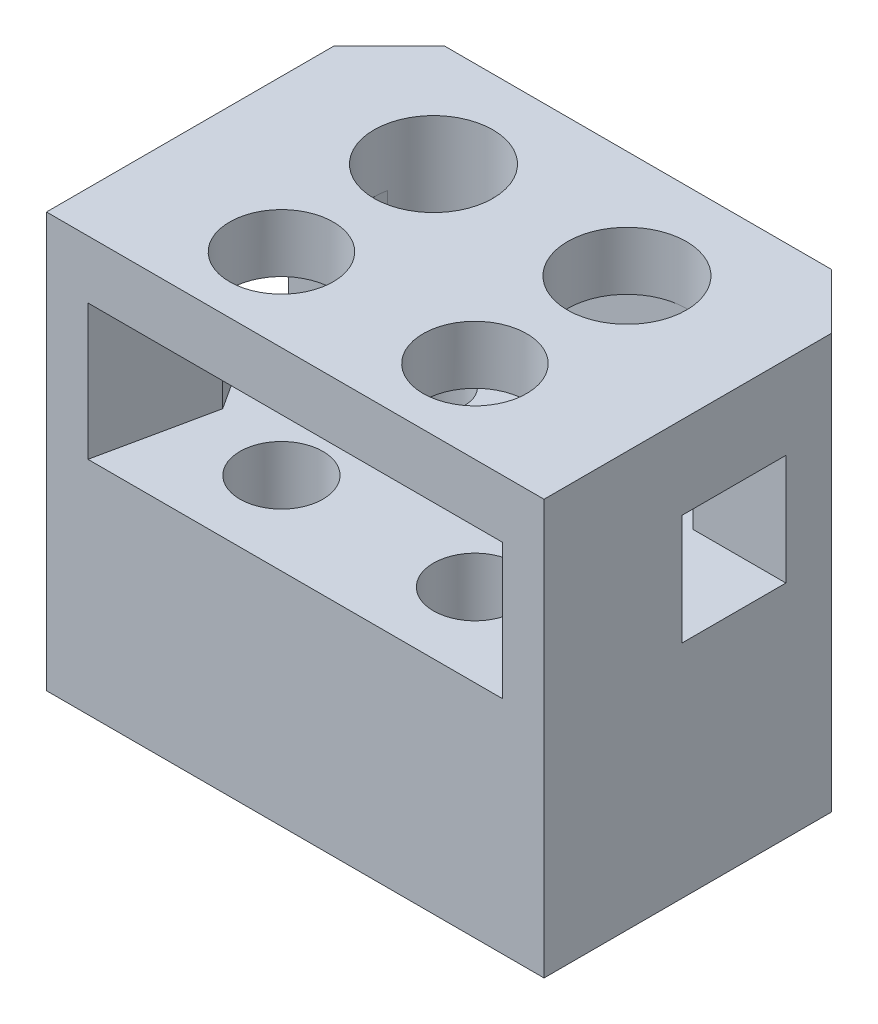
SolidWorks part; units mm, degrees
ref_plane "Front Plane" through (0, 0, 0) normal (0, 0, 1) x (1, 0, 0)
ref_plane "Top Plane" through (0, 0, 0) normal (0, 1, 0) x (1, 0, 0)
ref_plane "Right Plane" through (0, 0, 0) normal (1, 0, 0) x (0, 0, -1)
sketch "Sketch1" plane through (0, 0, 0) normal (0, 1, 0) x (1, 0, 0)
  line L0 (0, 0) -> (0, 17) construction
  line L1 (-7, 17) -> (7, 17) construction
  line L2 (-18, 0) -> (18, 0)
  line L3 (18, 0) -> (18, 20.8)
  line L4 (18, 20.8) -> (14, 24.8)
  line L5 (14, 24.8) -> (-14, 24.8)
  line L6 (-18, 20.8) -> (-14, 24.8)
  line L7 (-18, 0) -> (-18, 20.8)
  line L8 (-7, 6) -> (7, 6) construction
  point P10 (0, 24.8)
  point P14 (0, 6)
  dimension "D1" = 14
  dimension "D2" = 17
  dimension "D3" = 11
  dimension "D4" = 3.8
  dimension "D5" = 45
  dimension "D6" = 28
  dimension "D7" = 14
  dimension "D8" = 11
extrude "Boss-Extrude1" add sketch "Sketch1" along normal blind 30
sketch "Sketch2" plane through (0, 0, 0) normal (1, 0, 0) x (0, 0, -1)
  line L0 (0, 30) -> (0, 0) construction
  line L1 (0, 25.8) -> (22, 25.8)
  line L2 (0, 25.8) -> (0, 16)
  line L3 (0, 16) -> (22, 16)
  line L4 (22, 25.8) -> (22, 16)
  line L5 (11, 16) -> (11, 25.8) construction
  line L6 (0, 20.9) -> (22, 20.9) construction
  line L7 (0, 0) -> (20.8, 0) construction
  point P284 (11, 20.9)
  dimension "D1" = 16
  dimension "D2" = 9.8
  dimension "D3" = 5
extrude "Cut-Extrude1" [suppressed] cut sketch "Sketch2" against normal mid plane 27
ref_plane "Plane1" through (0, 16, 0) normal (0, 1, 0) x (1, 0, 0)
sketch "Sketch7" plane through (0, 16, 0) normal (0, 1, 0) x (1, 0, 0)
  line L0 (-7, 21.3) -> (7, 21.3)
  line L1 (11.2065, 17.8919) -> (15, 0)
  line L2 (-18, 0) -> (18, 0) construction
  line L3 (15, 0) -> (-15, 0)
  line L4 (0, 0) -> (0, 21.3) construction
  line L5 (-11.2065, 17.8919) -> (-15, 0)
  arc A0 (7, 21.3) -> (11.2065, 17.8919) centre (7, 17) cw
  arc A1 (-7, 21.3) -> (-11.2065, 17.8919) centre (-7, 17) ccw
  dimension "D2" = 4.3
  dimension "D1" = 30
extrude "Cut-Extrude2" cut sketch "Sketch7" along normal blind 9.8
hole_wizard "CBORE for M4 SBHCS1" positions "Sketch3" profile "Sketch4" counterbore size "M4" standard "ANSI Metric" end condition through all
sketch "Sketch3" plane through (0, 30, 0) normal (0, 1, 0) x (1, 0, 0)
  point P0 (-7, 17)
  point P3 (7, 17)
sketch "Sketch4" plane through (-7, 30, -17) normal (1, 0, 0) x (0, 0, 1)
  line L0 (0, 0) -> (0, 30)
  line L1 (0, 30) -> (2.25, 30)
  line L3 (2.25, 30) -> (2.25, 8)
  line L4 (2.25, 8) -> (4.3, 8)
  line L5 (4.3, 8) -> (4.3, 0)
  line L7 (4.3, 0) -> (0, 0)
  line L11 (0, -6.35) -> (0, 107.95) construction
  dimension "Thru Hole Dia." = 4.5
  dimension "Thru Hole Depth" = 30
  dimension "C'Bore Dia." = 8.6
  dimension "C'Bore Depth" = 8
hole_wizard "Ø6.0 (6) Diameter Hole1" positions "Sketch5" profile "Sketch6" hole size "Ø6.0" standard "ANSI Metric" end condition through all
sketch "Sketch5" plane through (0, 30, 0) normal (0, 1, 0) x (1, 0, 0)
  point P0 (-7, 6)
  point P3 (7, 6)
sketch "Sketch6" plane through (-7, 30, -6) normal (1, 0, 0) x (0, 0, 1)
  line L0 (0, 0) -> (0, 30)
  line L1 (0, 30) -> (3, 30)
  line L2 (3, 30) -> (3, 0)
  line L5 (3, 0) -> (0, 0)
  line L11 (0, -6.35) -> (0, 107.95) construction
  dimension "Thru Hole Dia." = 6
  dimension "Thru Hole Depth" = 30
sketch "Sketch9" plane through (0, 0, 0) normal (1, 0, 0) x (0, 0, -1)
  line L1 (10, 24) -> (17.5, 24)
  line L2 (10, 24) -> (10, 16)
  line L3 (10, 16) -> (17.5, 16)
  line L4 (17.5, 24) -> (17.5, 16)
  line L5 (13.75, 16) -> (13.75, 24) construction
  line L6 (10, 20) -> (17.5, 20) construction
  line L7 (9, 16) -> (3, 16) construction
  point P240 (13.75, 20)
  dimension "D1" = 4
  dimension "D2" = 7.5
  dimension "D3" = 8
extrude "Cut-Extrude3" cut sketch "Sketch9" against normal through all both and the other way through all
chamfer "Chamfer1" distance 2 angle 45 2 edges at (-12.8798, 20, -10) (12.8798, 20, -10)
hole_wizard "Ø7.5 (7.5) Diameter Hole1" positions "Sketch10" profile "Sketch11" hole size "Ø7.5" standard "ANSI Metric"
sketch "Sketch10" plane through (0, 30, 0) normal (0, 1, 0) x (1, 0, 0)
  point P0 (-7, 6)
  point P3 (7, 6)
sketch "Sketch11" plane through (-7, 30, -6) normal (1, 0, 0) x (0, 0, 1)
  line L0 (0, 0) -> (0, 9.2532)
  line L1 (0, 9.2532) -> (3.75, 7)
  line L2 (3.75, 7) -> (3.75, 0)
  line L5 (3.75, 0) -> (0, 0)
  line L10 (0, 9.2532) -> (-3.75, 7) construction
  line L11 (0, -6.35) -> (0, 107.95) construction
  dimension "Hole Dia." = 7.5
  dimension "Hole Depth" = 7
  dimension "Drill Angle" = 118
